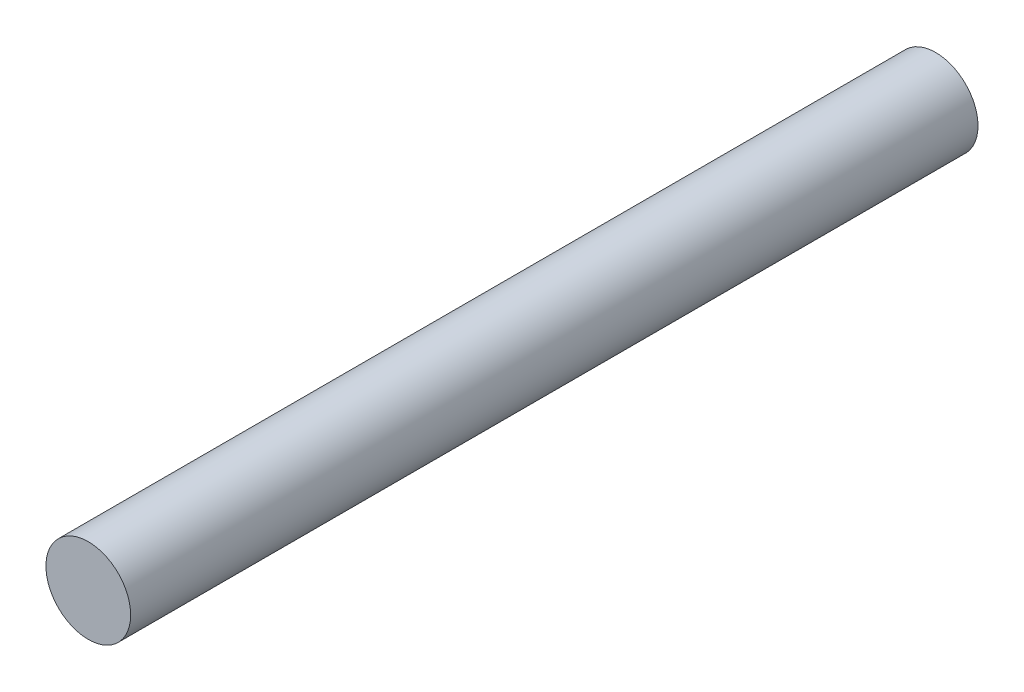
SolidWorks part; units mm, degrees
ref_plane "Front Plane" through (0, 0, 0) normal (0, 0, 1) x (1, 0, 0)
ref_plane "Top Plane" through (0, 0, 0) normal (0, 1, 0) x (1, 0, 0)
ref_plane "Right Plane" through (0, 0, 0) normal (1, 0, 0) x (0, 0, -1)
sketch "Sketch1" plane through (0, 0, 0) normal (0, 0, 1) x (1, 0, 0)
  circle A0 centre (0, 0) radius 1.5
  dimension "D1" = 3
extrude "Boss-Extrude1" add sketch "Sketch1" along normal blind 30
